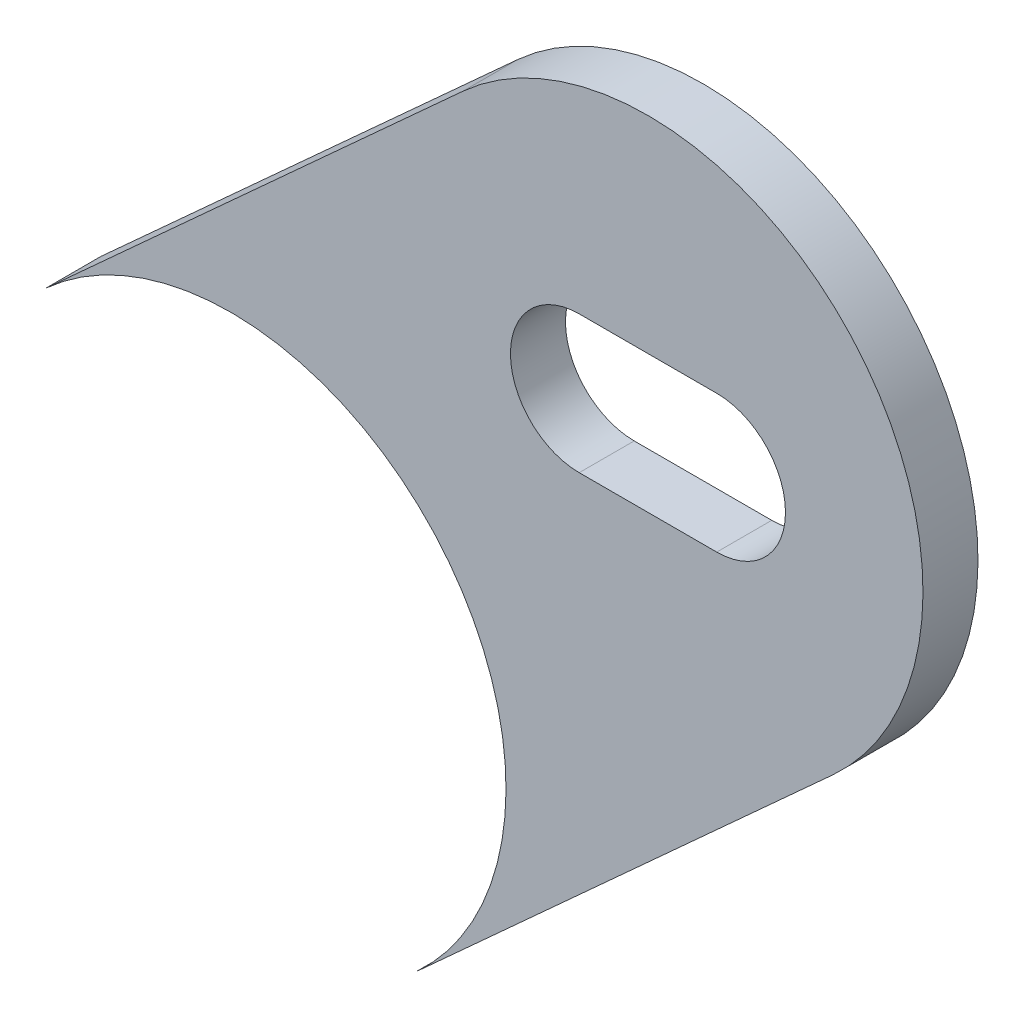
SolidWorks part; units mm, degrees
material "AISI 4130 Steel, normalized at 870C"
ref_plane "Front Plane" through (0, 0, 0) normal (0, 0, 1) x (1, 0, 0)
ref_plane "Top Plane" through (0, 0, 0) normal (0, 1, 0) x (1, 0, 0)
ref_plane "Right Plane" through (0, 0, 0) normal (1, 0, 0) x (0, 0, -1)
sketch "Sketch2" plane through (0, 0, 0) normal (0, 0, 1) x (1, 0, 0)
  line L0 (-132.1732, -84.5824) -> (-112.919, -67.08)
  line L1 (-115.0881, -103.3776) -> (-95.8339, -85.8752)
  line L5 (-107.5514, -79.6526) -> (-101.2014, -79.6526)
  line L6 (-107.5514, -79.6526) -> (-107.5514, -73.3026) construction
  line L7 (-107.5514, -73.3026) -> (-101.2014, -73.3026)
  line L8 (-101.2014, -79.6526) -> (-101.2014, -73.3026) construction
  line L9 (-107.5514, -79.6526) -> (-101.2014, -73.3026) construction
  line L10 (-107.5514, -73.3026) -> (-101.2014, -79.6526) construction
  circle A1 centre (-123.6307, -93.98) radius 12.7 construction
  arc A4 (-95.8339, -85.8752) -> (-112.919, -67.08) centre (-104.3764, -76.4776) ccw
  arc A7 (-132.1732, -84.5824) -> (-115.0881, -103.3776) centre (-123.6307, -93.98) cw
  circle A8 centre (-104.3764, -76.4776) radius 3.175 construction
  arc A10 (-101.2014, -73.3026) -> (-101.2014, -79.6526) centre (-101.2014, -76.4776) cw
  arc A11 (-107.5514, -73.3026) -> (-107.5514, -79.6526) centre (-107.5514, -76.4776) ccw
  circle A12 centre (-123.6307, -93.98) radius 12.7 construction
  dimension "D2" = 6.35
  dimension "D3" = 3.175
  dimension "D4" = 12.7
extrude "Boss-Extrude3" add sketch "Sketch2" along normal blind 2.54 from offset 4.7625
